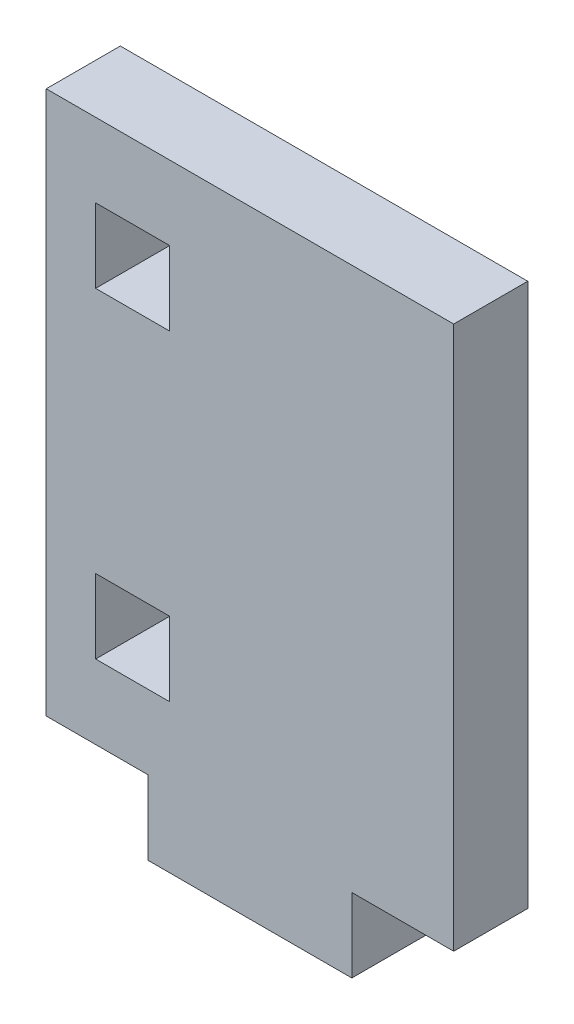
SolidWorks part; units mm, degrees
ref_plane "Front Plane" through (0, 0, 0) normal (0, 0, 1) x (1, 0, 0)
ref_plane "Top Plane" through (0, 0, 0) normal (0, 1, 0) x (1, 0, 0)
ref_plane "Right Plane" through (0, 0, 0) normal (1, 0, 0) x (0, 0, -1)
sketch "Sketch1" plane through (0, 0, 0) normal (0, 0, 1) x (1, 0, 0)
  line L1 (-8.25, -11) -> (8.25, -11)
  line L2 (-8.25, -11) -> (-8.25, 11)
  line L3 (-8.25, 11) -> (8.25, 11)
  line L4 (8.25, -11) -> (8.25, 11)
  point P0 (0, 0)
  dimension "D1" = 16.5
  dimension "D2" = 22
extrude "Boss-Extrude1" add sketch "Sketch1" along normal blind 3
sketch "Sketch2" plane through (0, -11, 0) normal (0, -1, 0) x (-1, 0, 0)
  line L0 (8.25, -3) -> (-8.25, -3) construction
  line L1 (4.125, -3) -> (-4.125, -3)
  line L2 (4.125, -3) -> (4.125, 0)
  line L3 (4.125, 0) -> (-4.125, 0)
  line L4 (-4.125, -3) -> (-4.125, 0)
  line L5 (8.25, 0) -> (-8.25, 0) construction
  line L6 (-8.25, -3) -> (-8.25, 0) construction
  dimension "D1" = 8.25
  dimension "D2" = 4.125
extrude "Boss-Extrude2" add sketch "Sketch2" along normal blind 3
sketch "Sketch3" plane through (0, 0, 3) normal (0, 0, 1) x (1, 0, 0)
  line L0 (-8.25, -11) -> (-4.125, -11) construction
  line L1 (-6.25, -5) -> (-3.25, -5)
  line L2 (-6.25, -5) -> (-6.25, -8)
  line L3 (-6.25, -8) -> (-3.25, -8)
  line L4 (-3.25, -5) -> (-3.25, -8)
  line L5 (-6.25, 8) -> (-3.25, 8)
  line L6 (-6.25, 8) -> (-6.25, 5)
  line L7 (-6.25, 5) -> (-3.25, 5)
  line L8 (-3.25, 8) -> (-3.25, 5)
  line L9 (8.25, 11) -> (-8.25, 11) construction
  line L10 (-8.25, 11) -> (-8.25, -11) construction
  dimension "D1" = 3
  dimension "D2" = 3
  dimension "D3" = 3
  dimension "D4" = 3
  dimension "D5" = 3
  dimension "D6" = 3
  dimension "D7" = 2
  dimension "D8" = 2
extrude "Cut-Extrude1" cut sketch "Sketch3" against normal blind 3
